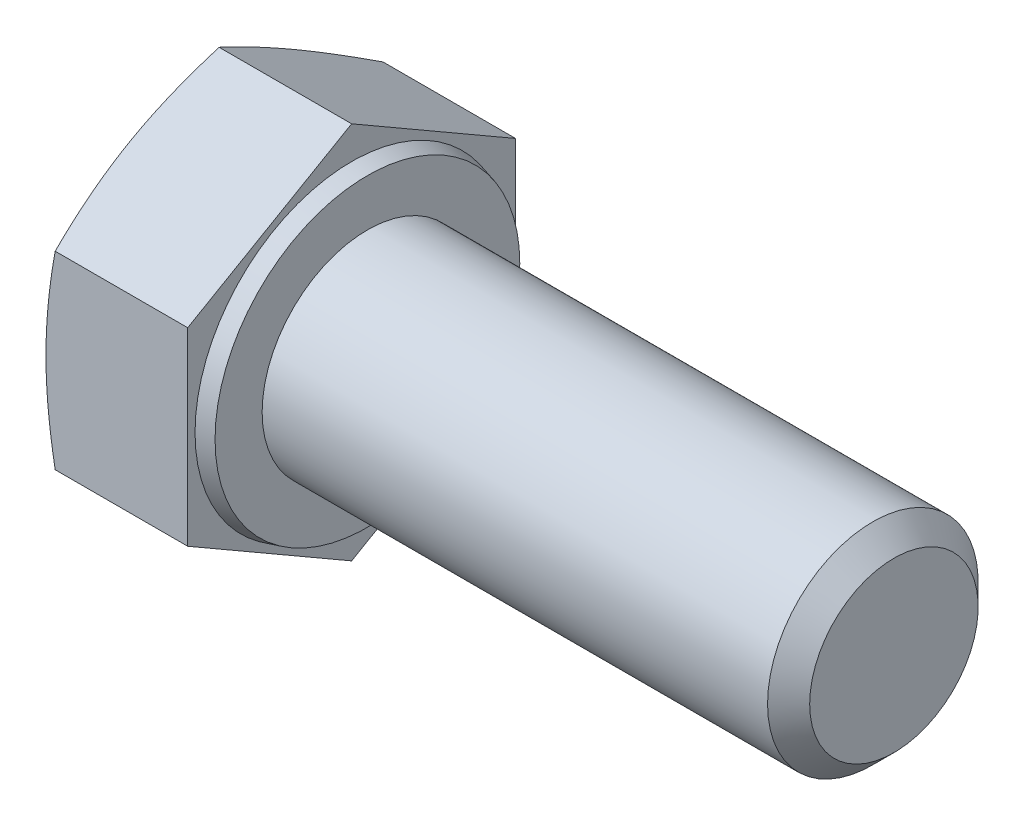
SolidWorks part; units mm, degrees
material "AISI 1020"
ref_plane "Спереди" through (0, 0, 0) normal (0, 0, 1) x (1, 0, 0)
ref_plane "Сверху" through (0, 0, 0) normal (0, 1, 0) x (1, 0, 0)
ref_plane "Справа" through (0, 0, 0) normal (1, 0, 0) x (0, 0, -1)
sketch "Эскиз1" plane through (0, 0, 0) normal (0, 0, 1) x (1, 0, 0)
  line L0 (-1000, 0) -> (49000, 0) construction
  line L1 (-5.45, 0) -> (-5.45, 7.19)
  line L2 (-5.45, 7.19) -> (0, 7.19)
  line L3 (0, 7.19) -> (0, 5.949)
  line L4 (0.6, 4) -> (20.6, 4)
  line L5 (20.6, 4) -> (20.6, 0)
  line L6 (-5.45, 0) -> (20.6, 0)
  line L7 (0, 5.949) -> (0.6, 5.7882)
  line L8 (0.6, 5.7882) -> (0.6, 4)
  line L9 (0.5, 0) -> (0.5, 5.815) construction
  dimension "_d" = 8
  dimension "D1" = 20
  dimension "D5" = 14.38
  dimension "D2" = 0.6
  dimension "D3" = 5.45
  dimension "D4" = 0.1
  dimension "D6" = 11.63
  dimension "D7" = 75
revolve "Повернуть1" add sketch "Эскиз1" angle 360 about L0
sketch "Эскиз2" plane through (-5.45, 0, 0) normal (-1, 0, 0) x (0, 0, 1)
  line L1 (0, -7.19) -> (6.2267, -3.595)
  line L2 (6.2267, -3.595) -> (6.2267, 3.595)
  line L3 (6.2267, 3.595) -> (0, 7.19)
  line L4 (0, 7.19) -> (-6.2267, 3.595)
  line L5 (-6.2267, 3.595) -> (-6.2267, -3.595)
  line L6 (-6.2267, -3.595) -> (0, -7.19)
  circle A0 centre (0, 0) radius 6.2267 construction
  circle A1 centre (0, 0) radius 7.19 construction
extrude "Вырез-Вытянуть1" cut sketch "Эскиз2" against normal through all flip side to cut
sketch "Эскиз4" plane through (0, 0, 0) normal (0, 0, 1) x (1, 0, 0)
  line L0 (-1000, 0) -> (49000, 0) construction
  line L1 (-5.45, 6.0468) -> (-5.0339, 7.19)
  line L2 (-5.0339, 7.19) -> (-5.45, 7.19)
  line L3 (-5.45, 7.19) -> (-5.45, 6.0468)
  line L4 (-5.45, 3.595) -> (-5.45, 7.19) construction
  line L6 (0, 7.19) -> (-5.45, 7.19) construction
  dimension "D1" = 20
  dimension "D2" = 12.0935
revolve "Вырез-Повернуть1" cut sketch "Эскиз4" angle 360 about L0
chamfer "Фаска1" distance 0.8 angle 45 1 edges at (20.6, 0, 4)
equation "\"l\"= 20'длина болта"
equation "\"_d\"= 8'диаметр болта"
equation "\"b\"= 20'длина резьбы"
equation "\"k\"= 5.45'толщина шляпки"
equation "\"e\"= 14.38'диаметр головки описанный"
equation "\"S\"= 12.73'размер под ключ"
equation "\"_d@Эскиз1\"=\"_d\""
equation "\"dw\"= 11.63"
equation "\"da\"= 9.78"
equation "\"с\"= 0.6"
equation "\"D1@Эскиз1\"=\"l\""
equation "\"D5@Эскиз1\"=\"e\""
equation "\"D2@Эскиз1\"=\"с\""
equation "\"D3@Эскиз1\"=\"k\""
equation "\"D2@Эскиз4\"=\"S\"*0.95"
equation "\"D1@Фаска1\"=\"_d\"/10"
equation "\"D6@Эскиз1\"=\"dw\""
